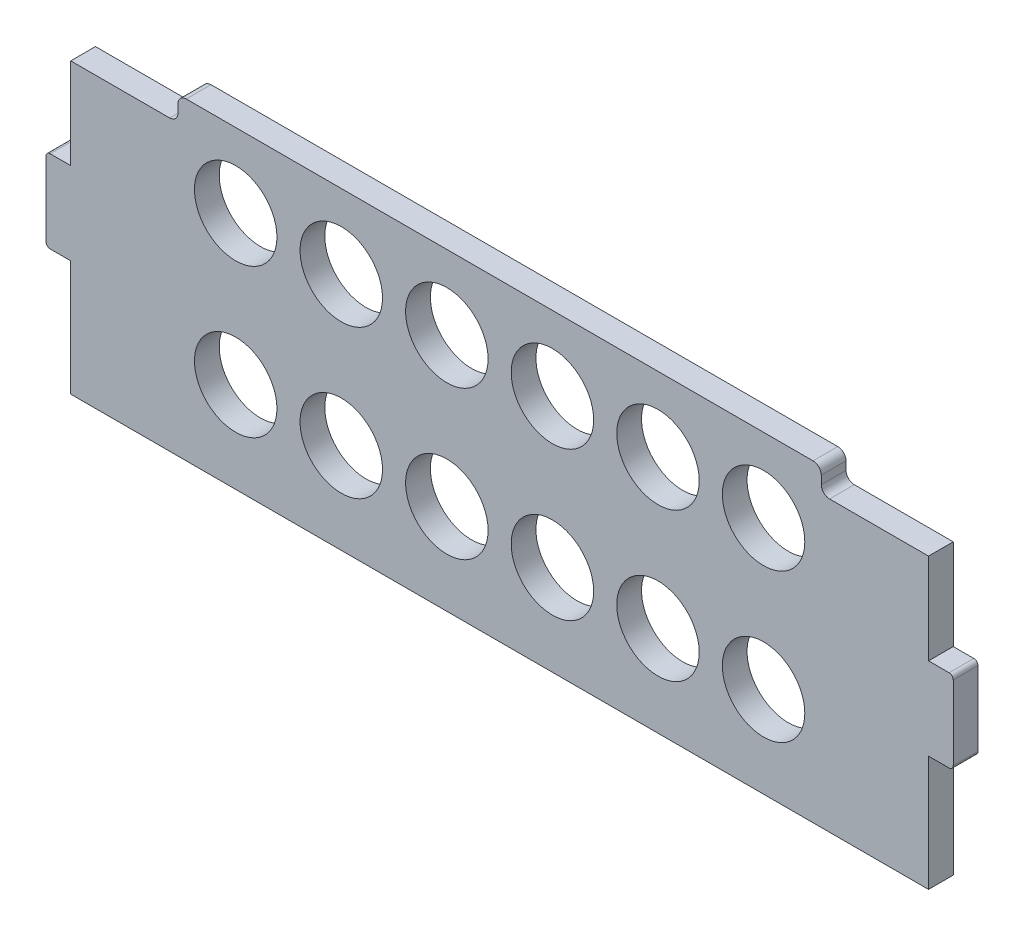
SolidWorks part; units mm, degrees
ref_plane "Спереди" through (0, 0, 0) normal (0, 0, 1) x (1, 0, 0)
ref_plane "Сверху" through (0, 0, 0) normal (0, 1, 0) x (1, 0, 0)
ref_plane "Справа" through (0, 0, 0) normal (1, 0, 0) x (0, 0, -1)
sketch "Эскиз1" plane through (0, 0, 0) normal (0, 0, 1) x (1, 0, 0)
  line L0 (0, 0) -> (0, 25.1439) construction
  line L1 (-52, 19) -> (52, 19)
  line L2 (-52, 19) -> (-52, -19)
  line L3 (-52, -19) -> (52, -19)
  line L4 (52, 19) -> (52, -19)
  line L5 (-52, 19) -> (52, -19) construction
  line L6 (-52, -19) -> (52, 19) construction
  line L7 (52, 5) -> (55, 5)
  line L8 (52, 5) -> (52, -5)
  line L9 (52, -5) -> (55, -5)
  line L10 (55, 5) -> (55, -5)
  line L11 (52, 5) -> (55, -5) construction
  line L12 (52, -5) -> (55, 5) construction
  line L13 (-52, -5) -> (-55, 5) construction
  line L14 (-52, 5) -> (-55, -5) construction
  line L15 (-55, 5) -> (-55, -5)
  line L16 (-52, -5) -> (-55, -5)
  line L17 (-52, 5) -> (-52, -5)
  line L18 (-52, 5) -> (-55, 5)
  line L19 (-52, 16) -> (-39, 16)
  line L20 (-39, 16) -> (-39, 19)
  line L21 (52, 16) -> (39, 16)
  line L22 (39, 16) -> (39, 19)
  circle A0 centre (-32, 10) radius 5
  circle A1 centre (-19.2, 10) radius 5
  circle A2 centre (-6.4, 10) radius 5
  circle A3 centre (6.4, 10) radius 5
  circle A4 centre (19.2, 10) radius 5
  circle A5 centre (32, 10) radius 5
  circle A6 centre (-32, -8) radius 5
  circle A7 centre (-19.2, -8) radius 5
  circle A8 centre (-6.4, -8) radius 5
  circle A9 centre (6.4, -8) radius 5
  circle A10 centre (19.2, -8) radius 5
  circle A11 centre (32, -8) radius 5
  point P0 (0, 0)
  point P6 (53.5, 0)
  point P17 (-53.5, 0)
  point P31 (0, -18)
  dimension "D5" = 10
  dimension "D7" = 4
  dimension "D1" = 3
  dimension "D2" = 10
  dimension "D3" = 38
  dimension "D4" = 110
  dimension "D6" = 15
  dimension "D9" = 15
  dimension "D11" = 18
  dimension "D12" = 3
  dimension "D13" = 13
  dimension "D8" = 6
  dimension "D10" = 2
extrude "Бобышка-Вытянуть1" add sketch "Эскиз1" along normal blind 3 contours L4 L1 L2 L3 A11 A10 A9 A8 A7 A6 A5 A4 A3 A2 A1 A0 | L2 L18 L15 L16 | L10 L7 L4 L9
fillet "Скругление1" radius 0.5 4 edges at (-55, -5, 1.5) (-55, 5, 1.5) (55, 5, 1.5) (55, -5, 1.5)
fillet "Скругление2" radius 1 2 edges at (-39, 16, 1.5) (-39, 19, 1.5)
fillet "Скругление3" radius 1 2 edges at (39, 16, 1.5) (39, 19, 1.5)
